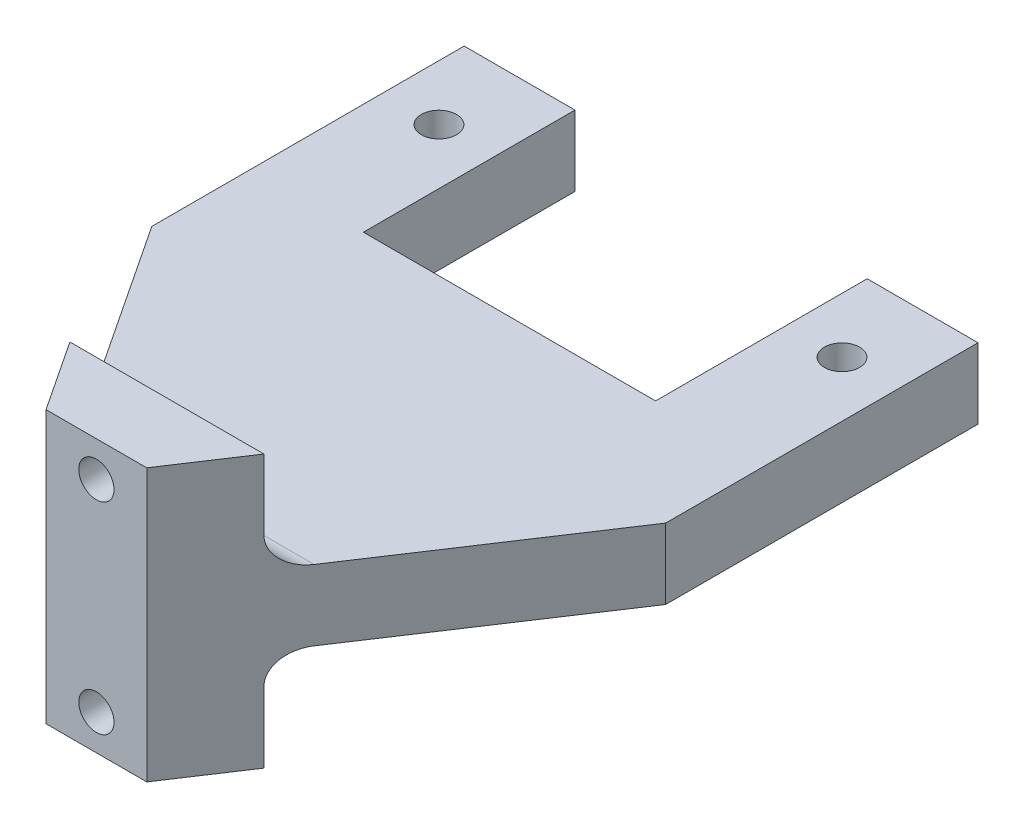
SolidWorks part; units mm, degrees
ref_plane "Front Plane" through (0, 0, 0) normal (0, 0, 1) x (1, 0, 0)
ref_plane "Top Plane" through (0, 0, 0) normal (0, 1, 0) x (1, 0, 0)
ref_plane "Right Plane" through (0, 0, 0) normal (1, 0, 0) x (0, 0, -1)
sketch "Sketch1" plane through (0, 0, 0) normal (0, 1, 0) x (1, 0, 0)
  line L1 (0, 0) -> (51, 0)
  line L2 (0, 0) -> (0, 62)
  line L3 (0, 62) -> (51, 62)
  line L4 (51, 0) -> (51, 62)
  dimension "D1" = 51
  dimension "D2" = 62
extrude "Boss-Extrude1" add sketch "Sketch1" along normal blind 7
sketch "Sketch2" plane through (0, 7, 0) normal (0, 1, 0) x (1, 0, 0)
  line L1 (0, 62) -> (11, 62) construction
  line L2 (0, 62) -> (0, 41) construction
  line L3 (0, 41) -> (11, 41) construction
  line L4 (11, 62) -> (11, 41) construction
  line L5 (51, 62) -> (40, 62) construction
  line L6 (51, 62) -> (51, 41) construction
  line L7 (51, 41) -> (40, 41) construction
  line L8 (40, 62) -> (40, 41) construction
  line L9 (11, 62) -> (40, 62)
  line L10 (11, 62) -> (11, 41)
  line L11 (11, 41) -> (40, 41)
  line L12 (40, 62) -> (40, 41)
  dimension "D1" = 21
  dimension "D3" = 11
  dimension "D4" = 11
extrude "Cut-Extrude1" cut sketch "Sketch2" against normal through all
sketch "Sketch9" plane through (0, 7, 0) normal (0, 1, 0) x (1, 0, 0)
  line L1 (0, 62) -> (5.5, 62) construction
  line L2 (0, 62) -> (0, 54) construction
  line L3 (0, 54) -> (5.5, 54) construction
  line L4 (5.5, 62) -> (5.5, 54) construction
  line L5 (40, 62) -> (45.5, 62) construction
  line L6 (40, 62) -> (40, 54) construction
  line L7 (40, 54) -> (45.5, 54) construction
  line L8 (45.5, 62) -> (45.5, 54) construction
  circle A0 centre (5.5, 54) radius 1.75
  circle A1 centre (45.5, 54) radius 1.75
  dimension "D3" = 3.5
  dimension "D4" = 3.5
  dimension "D1" = 8
  dimension "D2" = 5.5
extrude "Cut-Extrude4" cut sketch "Sketch9" against normal through all
sketch "Sketch11" plane through (0, 7, 0) normal (0, 1, 0) x (1, 0, 0)
  line L0 (25.5, 41) -> (25.5, 0) construction
  line L1 (11, 41) -> (40, 41) construction
  line L2 (0, 0) -> (51, 0) construction
  line L3 (20.5, 0) -> (30.5, 0) construction
  line L4 (20.5, 0) -> (0, 31)
  line L5 (0, 62) -> (0, 0) construction
  line L6 (30.5, 0) -> (51, 31)
  line L7 (51, 0) -> (51, 62) construction
  line L8 (0, 31) -> (0, 0)
  line L9 (0, 0) -> (20.5, 0)
  line L10 (51, 31) -> (51, 0)
  line L11 (51, 0) -> (30.5, 0)
  point P8 (25.5, 0)
  dimension "D1" = 10
  dimension "D2" = 10
extrude "Cut-Extrude5" cut sketch "Sketch11" against normal through all
sketch "Sketch12" plane through (0, 7, 0) normal (0, 1, 0) x (1, 0, 0)
  line L0 (30.5, 0) -> (20.5, 0)
  line L1 (20.5, 0) -> (15.871, 7)
  line L2 (20.5, 0) -> (0, 31) construction
  line L3 (15.871, 7) -> (35.129, 7)
  line L4 (51, 31) -> (30.5, 0) construction
  line L5 (35.129, 7) -> (30.5, 0)
  dimension "D1" = 7
extrude "Boss-Extrude4" add sketch "Sketch12" along normal blind 10
ref_plane "Plane1" through (0, 3.5, 0) normal (0, 1, 0) x (1, 0, 0)
mirror "Mirror1" about plane through (0, 3.5, 0) normal (0, 1, 0) of "Boss-Extrude4"
sketch "Sketch13" plane through (0, 0, 0) normal (0, 0, 1) x (1, 0, 0)
  line L0 (25.5, 17) -> (25.5, -10) construction
  line L1 (20.5, 17) -> (30.5, 17) construction
  line L2 (20.5, -10) -> (30.5, -10) construction
  line L3 (20.5, 3.5) -> (30.5, 3.5) construction
  line L4 (20.5, -10) -> (20.5, 17) construction
  line L5 (30.5, -10) -> (30.5, 17) construction
  line L6 (25.5, -6.5) -> (25.5, 13.5) construction
  circle A0 centre (25.5, 13.5) radius 1.75
  circle A1 centre (25.5, -6.5) radius 1.75
  point P14 (25.5, 3.5)
  dimension "D2" = 3.5
  dimension "D3" = 3.5
  dimension "D1" = 20
extrude "Cut-Extrude6" cut sketch "Sketch13" against normal through all
fillet "Fillet1" radius 3 2 edges at (25.5, 7, -7) (25.5, 0, -7)
